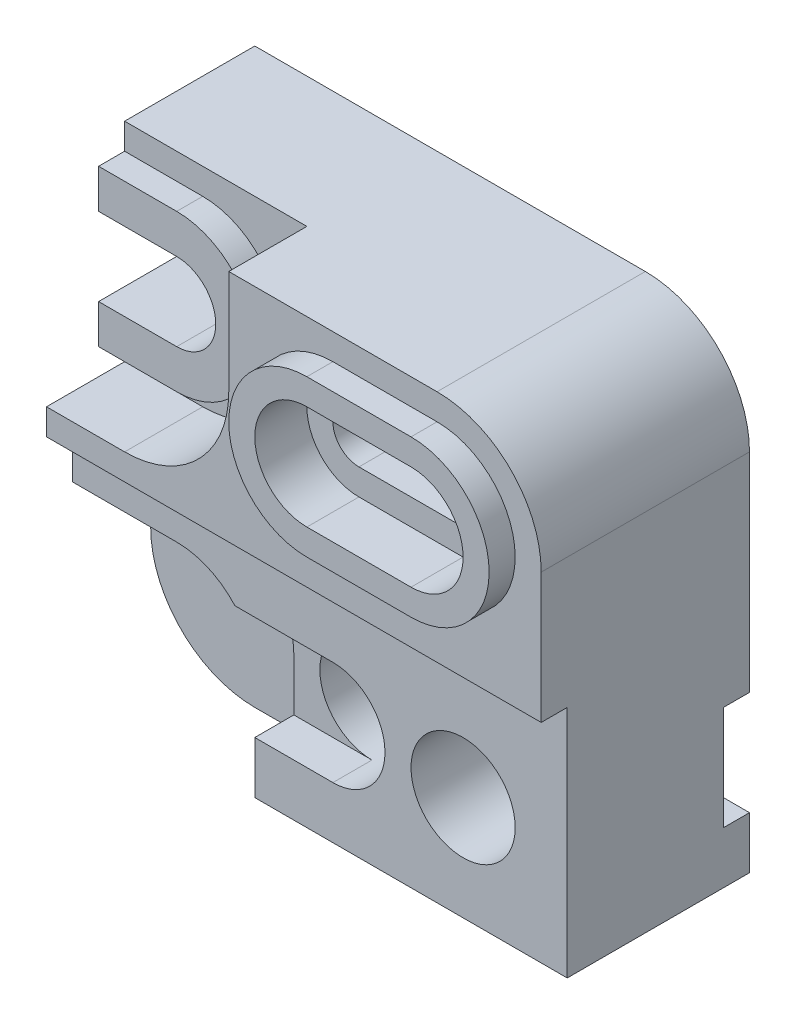
SolidWorks part; units mm, degrees
ref_plane "Front Plane" through (0, 0, 0) normal (0, 0, 1) x (1, 0, 0)
ref_plane "Top Plane" through (0, 0, 0) normal (0, 1, 0) x (1, 0, 0)
ref_plane "Right Plane" through (0, 0, 0) normal (1, 0, 0) x (0, 0, -1)
sketch "Sketch1" plane through (0, 0, 0) normal (0, 0, 1) x (1, 0, 0)
  line L1 (0, 0) -> (190, 0)
  line L2 (0, 0) -> (0, 180)
  line L3 (0, 180) -> (190, 180)
  line L4 (190, 0) -> (190, 180)
  dimension "D1" = 190
  dimension "D2" = 180
extrude "Boss-Extrude1" add sketch "Sketch1" along normal blind 70
sketch "Sketch2" plane through (0, 0, 0) normal (0, 0, -1) x (-1, 0, 0)
  line L0 (-150, 140) -> (-110, 140) construction
  line L1 (-150, 150) -> (-110, 150)
  line L2 (-150, 130) -> (-110, 130)
  arc A0 (-150, 150) -> (-150, 130) centre (-150, 140) ccw
  arc A1 (-110, 130) -> (-110, 150) centre (-110, 140) ccw
  point P2 (-130, 140)
  dimension "D1" = 40
  dimension "D2" = 10
  dimension "D3" = 40
  dimension "D4" = 40
extrude "Cut-Extrude1" cut sketch "Sketch2" against normal blind 70
sketch "Sketch3" plane through (0, 0, 0) normal (0, 0, -1) x (-1, 0, 0)
  line L0 (-110, 140) -> (-150, 140) construction
  line L1 (-110, 120) -> (-150, 120)
  line L2 (-110, 160) -> (-150, 160)
  arc A0 (-110, 120) -> (-110, 160) centre (-110, 140) ccw
  arc A1 (-150, 160) -> (-150, 120) centre (-150, 140) ccw
  point P4 (-130, 140)
  dimension "D1" = 40
extrude "Cut-Extrude2" cut sketch "Sketch3" against normal blind 20
sketch "Sketch4" plane through (0, 0, 70) normal (0, 0, 1) x (1, 0, 0)
  line L0 (190, 180) -> (0, 180) construction
  line L1 (190, 0) -> (190, 180) construction
  line L2 (150, 180) -> (190, 180)
  line L3 (190, 180) -> (190, 140)
  line L4 (0, 180) -> (0, 0) construction
  line L5 (0, 40) -> (0, 0)
  line L6 (0, 0) -> (40, 0)
  arc A0 (150, 180) -> (190, 140) centre (150, 140) cw
  arc A1 (0, 40) -> (40, 0) centre (40, 40) ccw
  dimension "D1" = 40
  dimension "D3" = 40
  dimension "D2" = 40
  dimension "D4" = 40
  dimension "D5" = 40
extrude "Cut-Extrude4" cut sketch "Sketch4" against normal blind 116
sketch "Sketch5" plane through (0, 0, 70) normal (0, 0, 1) x (1, 0, 0)
  line L0 (0, 155) -> (30, 155)
  line L1 (0, 180) -> (0, 40) construction
  line L2 (0, 125) -> (30, 125)
  line L3 (0, 155) -> (0, 125)
  arc A0 (30, 155) -> (30, 125) centre (30, 140) cw
  line M5 (0, 180) -> (0, 40)
  dimension "D5" = 15
  dimension "D1" = 30
  dimension "D2" = 30
  dimension "D3" = 25
  dimension "D4" = 30
extrude "Cut-Extrude5" cut sketch "Sketch5" against normal blind 116 contours A0 L0 L2 M5
sketch "Sketch6" plane through (0, 0, 0) normal (-1, 0, 0) x (0, 0, 1)
  line L1 (70, 180) -> (50, 180)
  line L2 (70, 180) -> (70, 90)
  line L3 (70, 90) -> (50, 90)
  line L4 (50, 180) -> (50, 90)
  dimension "D1" = 20
  dimension "D2" = 90
extrude "Cut-Extrude6" cut sketch "Sketch6" against normal blind 242
sketch "Sketch7" plane through (0, 0, 50) normal (0, 0, 1) x (1, 0, 0)
  line L0 (150, 140) -> (110, 140) construction
  line L1 (150, 110) -> (110, 110)
  line L2 (150, 170) -> (110, 170)
  arc A0 (150, 110) -> (150, 170) centre (150, 140) ccw
  arc A1 (110, 170) -> (110, 110) centre (110, 140) ccw
  point P4 (130, 140)
  dimension "D1" = 60
extrude "Boss-Extrude2" add sketch "Sketch7" along normal blind 10
sketch "Sketch11" plane through (0, 0, 50) normal (0, 0, -1) x (-1, 0, 0)
  line L0 (-150, 140) -> (-110, 140) construction
  line L1 (-150, 150) -> (-110, 150)
  line L2 (-150, 130) -> (-110, 130)
  arc A0 (-150, 150) -> (-150, 130) centre (-150, 140) ccw
  arc A1 (-110, 130) -> (-110, 150) centre (-110, 140) ccw
  point P4 (-130, 140)
  dimension "D1" = 20
extrude "Cut-Extrude12" cut sketch "Sketch11" against normal blind 20
sketch "Sketch12" plane through (0, 0, 50) normal (0, 0, 1) x (1, 0, 0)
  line L0 (0, 125) -> (30, 125) construction
  line L1 (30, 155) -> (0, 155)
  line L2 (30, 125) -> (0, 125)
  line L3 (0, 125) -> (0, 110)
  line L4 (0, 125) -> (0, 90) construction
  line L5 (0, 155) -> (0, 170)
  line L6 (0, 180) -> (0, 155) construction
  line L7 (0, 170) -> (30, 170)
  line L8 (0, 110) -> (30, 110)
  arc A0 (30, 155) -> (30, 125) centre (30, 140) cw
  arc A1 (30, 170) -> (30, 110) centre (30, 140) cw
  dimension "D3" = 30
  dimension "D1" = 15
  dimension "D2" = 15
extrude "Boss-Extrude4" add sketch "Sketch12" along normal blind 10
sketch "Sketch13" plane through (0, 0, 50) normal (0, 0, 1) x (1, 0, 0)
  line L0 (0, 180) -> (150, 180)
  line L1 (0, 180) -> (0, 170)
  line L2 (0, 180) -> (0, 170) construction
  line L3 (0, 110) -> (0, 100)
  line L4 (0, 110) -> (0, 90) construction
  line L5 (0, 100) -> (190, 100)
  line L6 (190, 140) -> (190, 90) construction
  line L7 (190, 100) -> (190, 140)
  line L8 (110, 110) -> (150, 110) construction
  line L9 (110, 170) -> (150, 170)
  line L10 (110, 110) -> (150, 110)
  line L11 (0, 170) -> (30, 170)
  line L12 (30, 110) -> (0, 110)
  arc A0 (150, 180) -> (190, 140) centre (150, 140) cw
  arc A1 (110, 170) -> (110, 110) centre (110, 140) ccw
  arc A2 (150, 170) -> (150, 110) centre (150, 140) cw
  arc A3 (150, 110) -> (150, 170) centre (150, 140) ccw construction
  arc A4 (30, 170) -> (30, 110) centre (30, 140) cw
  arc A5 (30, 110) -> (30, 170) centre (30, 140) ccw construction
  arc M1 (150, 170) -> (150, 110) centre (150, 140) cw
  line M2 (150, 110) -> (110, 110)
  arc M3 (110, 110) -> (110, 170) centre (110, 140) cw
  line M4 (110, 170) -> (150, 170)
  line M5 (30, 110) -> (0, 110)
  line M6 (0, 110) -> (0, 90)
  line M8 (190, 90) -> (190, 140)
  arc M9 (190, 140) -> (150, 180) centre (150, 140) ccw
  line M10 (150, 180) -> (0, 180)
  line M11 (0, 180) -> (0, 170)
  line M12 (0, 170) -> (30, 170)
  arc M13 (30, 170) -> (30, 110) centre (30, 140) cw
extrude "Boss-Extrude5" add sketch "Sketch13" along normal blind 30 contours L5 M6 M8 M9 M10 M11 M12 M13 M5 M4 M1 M2 M3
sketch "Sketch14" plane through (0, 0, 60) normal (0, 0, 1) x (1, 0, 0)
  line L0 (110, 140) -> (150, 140) construction
  line L1 (110, 170) -> (150, 170)
  line L2 (110, 110) -> (150, 110)
  arc A0 (110, 170) -> (110, 110) centre (110, 140) ccw
  arc A1 (150, 110) -> (150, 170) centre (150, 140) ccw
  point P4 (130, 140)
  dimension "D1" = 60
extrude "Cut-Extrude13" cut sketch "Sketch14" against normal blind 10
sketch "Sketch15" plane through (0, 0, 50) normal (0, 0, 1) x (1, 0, 0)
  line L1 (0, 100) -> (190, 100)
  line L2 (0, 100) -> (0, 90)
  line L3 (0, 90) -> (190, 90)
  line L4 (190, 100) -> (190, 90)
extrude "Boss-Extrude6" add sketch "Sketch15" along normal blind 30
sketch "Sketch16" plane through (0, 0, 80) normal (0, 0, 1) x (1, 0, 0)
  line L0 (0, 170) -> (0, 180)
  line L1 (0, 180) -> (150, 180)
  line L2 (0, 170) -> (30, 170)
  line L3 (0, 110) -> (30, 110)
  line L4 (0, 110) -> (0, 100)
  line L5 (0, 110) -> (0, 90) construction
  line L6 (0, 100) -> (190, 100)
  line L7 (190, 90) -> (190, 140) construction
  line L8 (190, 100) -> (190, 140)
  line L9 (70, 140) -> (70, 180)
  line L10 (0, 170) -> (30, 170)
  line L11 (30, 110) -> (0, 110)
  arc A0 (150, 180) -> (190, 140) centre (150, 140) cw
  arc A1 (30, 100) -> (70, 140) centre (30, 140) ccw
  arc A2 (30, 170) -> (30, 110) centre (30, 140) cw
  arc A3 (30, 110) -> (30, 170) centre (30, 140) ccw construction
  line M5 (0, 110) -> (0, 90)
  line M10 (0, 180) -> (0, 170)
  line M11 (0, 170) -> (30, 170)
  arc M12 (30, 170) -> (30, 110) centre (30, 140) cw
  line M13 (30, 110) -> (0, 110)
  dimension "D1" = 40
extrude "Cut-Extrude14" cut sketch "Sketch16" against normal blind 30 contours L6 A1 L9 L1 M10 M11 M12 M13 M5
ref_plane "Plane1" through (110, 120, 20) normal (-1, 0, 0) x (0, 0, 1)
sketch "Sketch18" plane through (0, 0, 50) normal (0, 0, 1) x (1, 0, 0)
  line L0 (150, 140) -> (110, 140) construction
  line L1 (150, 110) -> (110, 110)
  line L2 (150, 170) -> (110, 170)
  arc A0 (150, 110) -> (150, 170) centre (150, 140) ccw
  arc A1 (110, 170) -> (110, 110) centre (110, 140) ccw
  point P4 (130, 140)
  dimension "D1" = 60
extrude "Boss-Extrude7" add sketch "Sketch18" along normal blind 30
ref_plane "Plane2" through (150, 150, 50) normal (1, 0, 0) x (0, 0, -1)
sketch "Sketch20" plane through (0, 0, 80) normal (0, 0, 1) x (1, 0, 0)
  line L0 (110, 140) -> (150, 140) construction
  line L1 (110, 170) -> (150, 170)
  line L2 (110, 110) -> (150, 110)
  arc A0 (110, 170) -> (110, 110) centre (110, 140) ccw
  arc A1 (150, 110) -> (150, 170) centre (150, 140) ccw
  point P4 (130, 140)
  dimension "D1" = 60
extrude "Boss-Extrude8" add sketch "Sketch20" along normal blind 10
sketch "Sketch21" plane through (0, 0, 90) normal (0, 0, 1) x (1, 0, 0)
  line L0 (110, 140) -> (150, 140) construction
  line L1 (110, 160) -> (150, 160)
  line L2 (110, 120) -> (150, 120)
  arc A0 (110, 160) -> (110, 120) centre (110, 140) ccw
  arc A1 (150, 120) -> (150, 160) centre (150, 140) ccw
  point P4 (130, 140)
  dimension "D1" = 40
extrude "Cut-Extrude15" cut sketch "Sketch21" against normal blind 20
sketch "Sketch22" plane through (0, 0, 50) normal (0, 0, -1) x (-1, 0, 0)
  line L0 (-150, 140) -> (-110, 140) construction
  line L1 (-150, 150) -> (-110, 150)
  line L2 (-150, 130) -> (-110, 130)
  arc A0 (-150, 150) -> (-150, 130) centre (-150, 140) ccw
  arc A1 (-110, 130) -> (-110, 150) centre (-110, 140) ccw
  point P4 (-130, 140)
  dimension "D1" = 20
extrude "Cut-Extrude16" cut sketch "Sketch22" against normal blind 62
sketch "Sketch23" plane through (0, 0, 70) normal (0, 0, 1) x (1, 0, 0)
  line L0 (0, 40) -> (0, 70)
  line L1 (0, 90) -> (0, 40) construction
  line L2 (0, 70) -> (40, 70)
  line L3 (70, 40) -> (70, 0)
  line L4 (40, 0) -> (190, 0) construction
  line L5 (70, 0) -> (40, 0)
  arc A0 (40, 70) -> (70, 40) centre (40, 40) cw
  arc A1 (0, 40) -> (40, 0) centre (40, 40) ccw
  arc A2 (0, 40) -> (40, 0) centre (40, 40) ccw construction
  dimension "D1" = 30
  dimension "D2" = 40
  dimension "D3" = 0
  dimension "D4" = 30
  dimension "D5" = 40
  dimension "D6" = 40
extrude "Cut-Extrude17" cut sketch "Sketch23" against normal blind 30
sketch "Sketch24" plane through (0, 0, 70) normal (0, 0, 1) x (1, 0, 0)
  line L0 (100, 60) -> (62.3607, 60)
  line L1 (100, 20) -> (70, 20)
  line L4 (70, 0) -> (70, 40) construction
  line L5 (70, 20) -> (70, 40)
  circle A0 centre (100, 40) radius 20
  arc A1 (70, 40) -> (40, 70) centre (40, 40) ccw construction
  arc A2 (40, 70) -> (70, 40) centre (40, 40) cw
  arc M1 (40, 70) -> (70, 40) centre (40, 40) cw
  line M2 (70, 40) -> (70, 0)
  dimension "D1" = 40
  dimension "D2" = 40
  dimension "D3" = 30
  dimension "D4" = 30
  dimension "D5" = 40
extrude "Cut-Extrude18" cut sketch "Sketch24" against normal blind 15 contours A0 L0 L1 M1 M2
sketch "Sketch25" plane through (0, 0, 70) normal (0, 0, 1) x (1, 0, 0)
  circle A0 centre (100, 40) radius 20
  circle A1 centre (150, 40) radius 20
  dimension "D2" = 40
  dimension "D1" = 50
  dimension "D3" = 40
extrude "Cut-Extrude19" cut sketch "Sketch25" against normal blind 50
sketch "Sketch26" plane through (0, 0, 40) normal (0, 0, 1) x (1, 0, 0)
  circle A0 centre (40, 40) radius 10
  dimension "D1" = 20
  dimension "D2" = 40
  dimension "D3" = 40
extrude "Cut-Extrude20" cut sketch "Sketch26" against normal blind 20
sketch "Sketch27" plane through (0, 0, 0) normal (0, 0, -1) x (-1, 0, 0)
  line L0 (0, 70) -> (-150, 70)
  line L1 (0, 125) -> (0, 40) construction
  line L2 (-13.5425, 10) -> (-150, 10)
  line L3 (0, 40) -> (0, 70)
  line L4 (-150, 70) -> (0, 70)
  arc A0 (-40, 0) -> (0, 40) centre (-40, 40) ccw construction
  circle A3 centre (-150, 40) radius 20 construction
  arc A4 (-150, 70) -> (-150, 10) centre (-150, 40) ccw
  arc A5 (0, 40) -> (-13.5425, 10) centre (-40, 40) cw
  arc M9 (-40, 0) -> (0, 40) centre (-40, 40) ccw
  line M10 (0, 40) -> (0, 125)
  dimension "D1" = 0
  dimension "D2" = 20
  dimension "D3" = 10
  dimension "D4" = 0
extrude "Cut-Extrude21" cut sketch "Sketch27" against normal blind 20 contours L0 A4 L2 M9 M10
sketch "Sketch28" plane through (190, 0, 0) normal (1, 0, 0) x (0, 0, -1)
  line L0 (0, 0) -> (0, 140) construction
  line L1 (0, 60) -> (-10, 60)
  line L2 (0, 60) -> (0, 20)
  line L3 (0, 20) -> (-10, 20)
  line L4 (-10, 60) -> (-10, 20)
  dimension "D1" = 20
  dimension "D2" = 40
  dimension "D3" = 10
extrude "Cut-Extrude22" cut sketch "Sketch28" against normal blind 59
